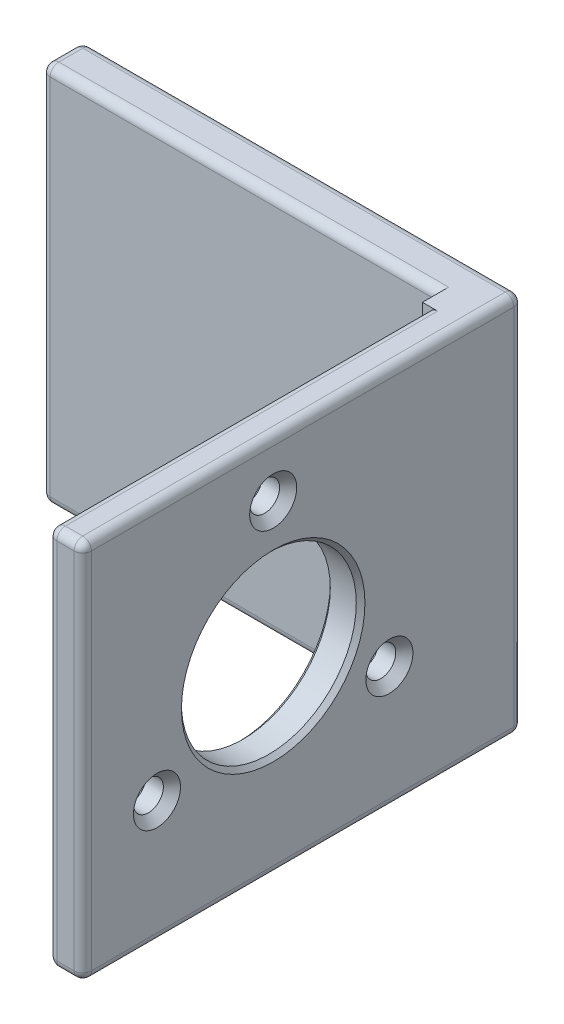
SolidWorks part; units mm, degrees
ref_plane "Front" through (0, 0, 0) normal (0, 0, 1) x (1, 0, 0)
ref_plane "Top" through (0, 0, 0) normal (0, 1, 0) x (1, 0, 0)
ref_plane "Right" through (0, 0, 0) normal (1, 0, 0) x (0, 0, -1)
sketch "Sketch2" plane through (0, 0, 0) normal (0, 1, 0) x (1, 0, 0)
  line L0 (0, 0) -> (-50.8, 0)
  line L1 (0, 0) -> (0, -50.8)
  dimension "D1" = 50.8
extrude "Extrude-Thin2" add sketch "Sketch2" along normal mid plane 44 thin thin type one direction wall 4.7625
sketch "Sketch3" plane through (-4.7625, 0, 0) normal (-1, 0, 0) x (0, 0, 1)
  line L0 (4.7625, 22) -> (50.8, 22) construction
  line L1 (6.8, 22) -> (50.8, 22)
  line L2 (6.8, 22) -> (6.8, -22)
  line L3 (6.8, -22) -> (50.8, -22)
  line L4 (50.8, 22) -> (50.8, -22)
  dimension "D1" = 44
extrude "Cut-Extrude1" cut sketch "Sketch3" against normal offset from surface (0.7625 mm away) 4 up to face at (0, 0, 25.4)
sketch "Sketch4" plane through (-4, 0, 0) normal (-1, 0, 0) x (0, 0, 1)
  line L0 (6.8, 22) -> (50.8, -22) construction
  circle A0 centre (28.8, 0) radius 10.1
  dimension "D1" = 20.2
extrude "Cut-Extrude2" cut sketch "Sketch4" against normal through all
sketch "Sketch5" plane through (-4, 0, 0) normal (-1, 0, 0) x (0, 0, 1)
  line L0 (28.8, 0) -> (28.8, 15.5)
  line L1 (28.8, 0) -> (42.2234, -7.75)
  line L2 (28.8, 0) -> (15.3766, -7.75)
  circle A0 centre (28.8, 0) radius 15.5
  dimension "D1" = 31
  dimension "D2" = 120
  dimension "D3" = 120
hole_wizard "#8-32 Tapped Hole1" positions "3DSketch1" profile "Sketch6" tap size "#8-32" standard "Ansi Inch" end condition through all
sketch3d "3DSketch1"
  point P0 (-4, 15.5, 28.8)
  point P3 (-4, -7.75, 42.2234)
  point P6 (-4, -7.75, 15.3766)
sketch "Sketch6" plane through (-4, 15.5, 28.8) normal (0, 1, 0) x (0, 0, 1)
  line L0 (0, 0) -> (0, 4)
  line L1 (0, 4) -> (2.7178, 4)
  line L2 (1.7272, 3.0094) -> (1.7272, 0.9906)
  line L3 (1.7272, 0.9906) -> (2.7178, 0)
  line L5 (2.7178, 0) -> (0, 0)
  line L6 (-1.7272, 0.9906) -> (-2.7178, 0) construction
  line L7 (2.7178, 4) -> (1.7272, 3.0094)
  line L8 (-2.7178, 4) -> (-1.7272, 3.0094) construction
  line L11 (0, -6.35) -> (0, 107.95) construction
  dimension "Thru Tap Drill Dia." = 3.4544
  dimension "Thru Tap Drill Depth" = 4
  dimension "Near C'Sink Dia." = 5.4356
  dimension "Near C'Sink Angle" = 90
  dimension "Far C'Sink Dia." = 5.4356
  dimension "Far C'Sink Angle" = 90
cosmetic thread "Hole Thread1" parameters "D2"=4.1656
cosmetic thread "Hole Thread2" parameters "D2"=4.1656
cosmetic thread "Hole Thread3" parameters "D2"=4.1656
chamfer "Chamfer2" distance 0.5 angle 45 2 edges at (0, 0, 38.9) (-4, 0, 38.9)
fillet "Fillet1" radius 1 17 edges at (0, 0, 0) (0, 0, 50.8) (0, -22, 25.4) (-25.4, -22, 0) (-50.8, 0, 0) (-25.4, 22, 0) (0, 22, 25.4) (-4, 22, 28.8) (-4, 0, 50.8) (-4, -22, 28.8) (-27.7812, -22, 4.7625) (-50.8, 0, 4.7625) (-27.7812, 22, 4.7625) (-2, -22, 50.8) (-2, 22, 50.8) (-50.8, -22, 2.3813) (-50.8, 22, 2.3813)
